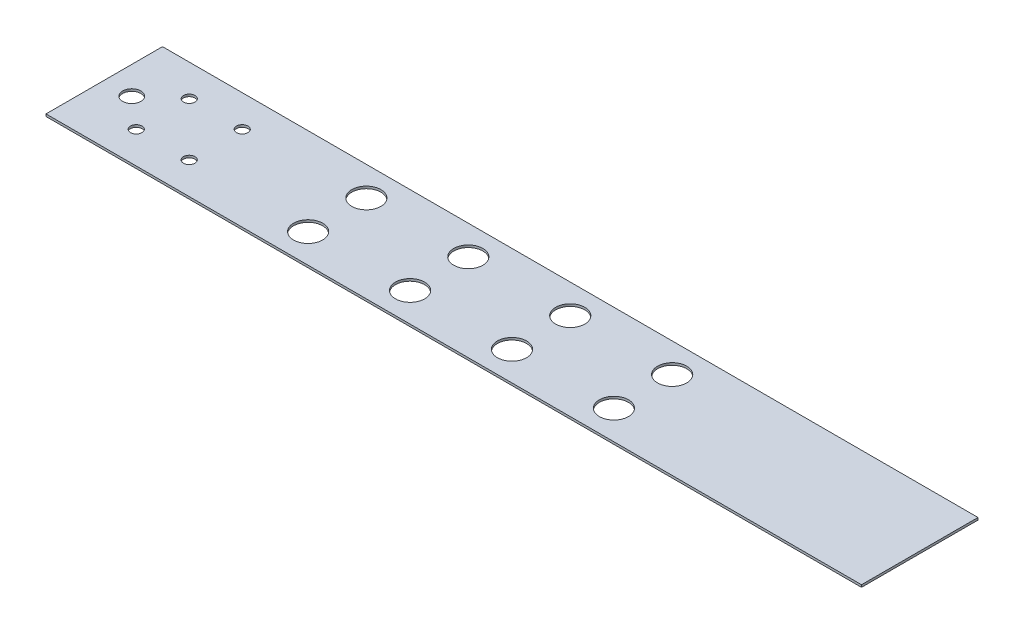
SolidWorks part; units mm, degrees
ref_plane "Plan de face" through (0, 0, 0) normal (0, 0, 1) x (1, 0, 0)
ref_plane "Plan de dessus" through (0, 0, 0) normal (0, 1, 0) x (1, 0, 0)
ref_plane "Plan de droite" through (0, 0, 0) normal (1, 0, 0) x (0, 0, -1)
sketch "Esquisse1" plane through (0, 0, 0) normal (0, 1, 0) x (1, 0, 0)
  line L1 (177.8, -25.4) -> (-177.8, -25.4)
  line L2 (177.8, -25.4) -> (177.8, 25.4)
  line L3 (177.8, 25.4) -> (-177.8, 25.4)
  line L4 (-177.8, -25.4) -> (-177.8, 25.4)
  line L5 (177.8, -25.4) -> (-177.8, 25.4) construction
  line L6 (177.8, 25.4) -> (-177.8, -25.4) construction
  point P0 (0, 0)
  dimension "D1" = 355.6
  dimension "D2" = 50.8
extrude "Boss.-Extru.1" add sketch "Esquisse1" along normal blind 1
sketch "Esquisse2" plane through (0, 1, 0) normal (0, 1, 0) x (1, 0, 0)
  line L0 (-177.8, 25.4) -> (-177.8, -25.4) construction
  circle A0 centre (-165.8, 0) radius 3.9687
  point P4 (0, 0)
  dimension "D1" = 7.9375
  dimension "D2" = 12
extrude "Enlèv. mat.-Extru.1" cut sketch "Esquisse2" against normal blind 1
sketch "Esquisse3" plane through (0, 1, 0) normal (0, 1, 0) x (1, 0, 0)
  line L0 (177.8, 25.4) -> (-177.8, 25.4) construction
  circle A0 centre (-152.3, 11.55) radius 2.5
  circle A1 centre (-129.2, 11.55) radius 2.5
  circle A2 centre (-129.2, -11.55) radius 2.5
  circle A3 centre (-152.3, -11.55) radius 2.5
  circle A4 centre (-165.8, 0) radius 3.9687 construction
  point P8 (0, 0)
  point P9 (0, 0)
  point P10 (0, 0)
  point P11 (0, 0)
  point P12 (0, 0)
  point P13 (0, 0)
  dimension "D1" = 5
  dimension "D2" = 23.1
  dimension "D3" = 23.1
  dimension "D4" = 13.85
  dimension "D5" = 13.5
extrude "Enlèv. mat.-Extru.2" cut sketch "Esquisse3" against normal blind 2
sketch "Esquisse4" plane through (0, 1, 0) normal (0, 1, 0) x (1, 0, 0)
  line L0 (-177.8, 25.4) -> (-177.8, -25.4) construction
  line L1 (-0.55, 0) -> (0.55, 0) construction
  line L2 (177.8, 25.4) -> (-177.8, 25.4) construction
  line L3 (-177.8, -25.4) -> (177.8, -25.4) construction
  circle A0 centre (-76.2, 12.7) radius 6.35
  circle A1 centre (12.7, 12.7) radius 6.35
  circle A2 centre (12.7, -12.7) radius 6.35
  circle A3 centre (-76.2, -12.7) radius 6.35
  circle A4 centre (-31.75, 12.7) radius 6.35
  circle A5 centre (57.15, 12.7) radius 6.35
  circle A6 centre (57.15, -12.7) radius 6.35
  circle A7 centre (-31.75, -12.7) radius 6.35
  point P20 (0, 0)
  point P21 (0, 0)
  dimension "D5" = 12.7
  dimension "D1" = 101.6
  dimension "D2" = 88.9
  dimension "D3" = 12.7
  dimension "D4" = 12.7
  dimension "D6" = 44.45
  dimension "D7" = 44.45
extrude "Enlèv. mat.-Extru.3" cut sketch "Esquisse4" against normal blind 2
